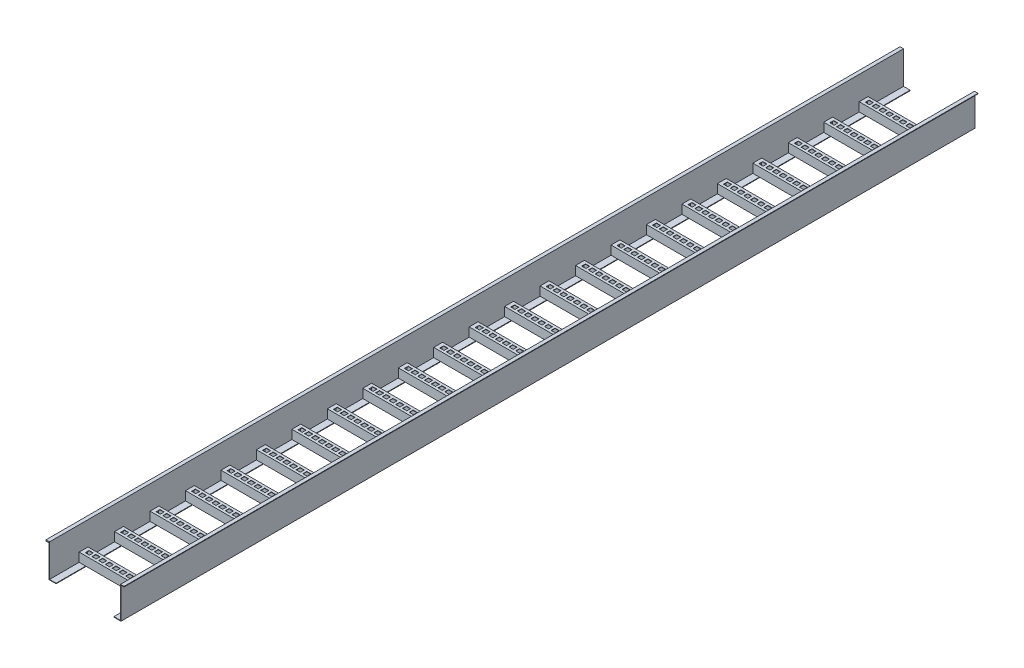
SolidWorks part; units mm, degrees
ref_plane "Alzado" through (0, 0, 0) normal (0, 0, 1) x (1, 0, 0)
ref_plane "Planta" through (0, 0, 0) normal (0, 1, 0) x (1, 0, 0)
ref_plane "Vista lateral" through (0, 0, 0) normal (1, 0, 0) x (0, 0, -1)
sketch "Croquis1" plane through (0, 0, 0) normal (0, 0, 1) x (1, 0, 0)
  line L0 (-55.6522, 79.8913) -> (-45.6522, 79.8913)
  line L1 (-45.6522, 79.8913) -> (-45.6522, -11.9155)
  line L2 (-45.6522, -11.9155) -> (154.3478, -11.9155)
  line L3 (154.3478, -11.9155) -> (154.3478, 76.1279)
  line L4 (154.3478, 76.1279) -> (164.3478, 76.1279)
  line L5 (164.3478, 76.1279) -> (164.3478, 74.6279)
  line L6 (164.3478, 74.6279) -> (155.8478, 74.6279)
  line L7 (155.8478, 74.6279) -> (155.8478, -13.4155)
  line L8 (155.8478, -13.4155) -> (-47.1522, -13.4155)
  line L9 (-47.1522, -13.4155) -> (-47.1522, 76.5154)
  line L10 (-47.1522, 76.5154) -> (-55.6522, 76.5154)
  line L11 (-55.6522, 76.5154) -> (-55.6522, 79.8913)
  line L12 (-27.1522, -11.9155) -> (-27.1522, -13.4155)
  line L13 (135.8478, -11.9155) -> (135.8478, -13.4155)
  dimension "D1" = 200
  dimension "D2" = 10
  dimension "D3" = 10
  dimension "D4" = 1.5
  dimension "D5" = 1.5
  dimension "D6" = 1.5
  dimension "D7" = 1.5
  dimension "D8" = 20
  dimension "D9" = 20
extrude "Saliente-Extruir1" add sketch "Croquis1" along normal blind 2408.5 contours L2 L13 L8 L7 L6 L5 L4 L3 | L12 L2 L1 L0 L11 L10 L9 L8
sketch "Croquis2" plane through (155.8478, 0, 0) normal (1, 0, 0) x (0, 0, -1)
  line L1 (-125, -11.9155) -> (-124, -11.9155)
  line L2 (-125, -11.9155) -> (-125, 13.0845)
  line L3 (-125, 13.0845) -> (-100, 13.0845)
  line L4 (-100, -11.9155) -> (-100, 13.0845)
  line L5 (-125, -11.9155) -> (-100, 13.0845) construction
  line L6 (-125, 13.0845) -> (-100, -11.9155) construction
  line L7 (0, 74.6279) -> (0, -13.4155) construction
  line L8 (-124, -11.9155) -> (-124, 12.0845)
  line L9 (-124, 12.0845) -> (-101, 12.0845)
  line L10 (-101, 12.0845) -> (-101, -11.9155)
  line L11 (-101, -11.9155) -> (-100, -11.9155)
  point P0 (-112.5, 0.5845)
  point P9 (-237.5, 0.5845)
  point P16 (-362.5, 0.5845)
  dimension "D1" = 25
  dimension "D2" = 25
  dimension "D3" = 1
  dimension "D4" = 100
  dimension "D5" = 1
  dimension "D6" = 1
extrude "Saliente-Extruir2" add sketch "Croquis2" against normal up to surface (201.5 mm away) up to face at (-45.6522, 33.9879, 1204.25)
pattern_linear "MatrizL1" count 23 spacing 100 along (0, 0, 1) of "Saliente-Extruir2"
sketch "Croquis3" plane through (0, 13.0845, 0) normal (0, 1, 0) x (1, 0, 0)
  line L0 (154.3478, -125) -> (154.3478, -100) construction
  line L1 (147.3478, -107) -> (135.3478, -107)
  line L2 (147.3478, -107) -> (147.3478, -118)
  line L3 (147.3478, -118) -> (135.3478, -118)
  line L4 (135.3478, -107) -> (135.3478, -118)
  line L5 (147.3478, -107) -> (135.3478, -118) construction
  line L6 (147.3478, -118) -> (135.3478, -107) construction
  line L7 (135.8478, -125) -> (154.3478, -125) construction
  line L8 (-45.6522, -100) -> (154.3478, -100) construction
  line L9 (-45.6522, -125) -> (154.3478, -125) construction
  line L10 (128.3478, -107) -> (116.3478, -107)
  line L11 (128.3478, -107) -> (128.3478, -118)
  line L12 (128.3478, -118) -> (116.3478, -118)
  line L13 (116.3478, -107) -> (116.3478, -118)
  line L14 (128.3478, -107) -> (116.3478, -118) construction
  line L15 (128.3478, -118) -> (116.3478, -107) construction
  line L17 (109.3478, -107) -> (97.3478, -107)
  line L18 (109.3478, -107) -> (109.3478, -118)
  line L19 (109.3478, -118) -> (97.3478, -118)
  line L20 (97.3478, -107) -> (97.3478, -118)
  line L21 (109.3478, -107) -> (97.3478, -118) construction
  line L22 (109.3478, -118) -> (97.3478, -107) construction
  line L23 (90.3478, -107) -> (78.3478, -107)
  line L24 (90.3478, -107) -> (90.3478, -118)
  line L25 (90.3478, -118) -> (78.3478, -118)
  line L26 (78.3478, -107) -> (78.3478, -118)
  line L27 (90.3478, -107) -> (78.3478, -118) construction
  line L28 (90.3478, -118) -> (78.3478, -107) construction
  line L29 (71.3478, -107) -> (59.3478, -107)
  line L30 (71.3478, -107) -> (71.3478, -118)
  line L31 (71.3478, -118) -> (59.3478, -118)
  line L32 (59.3478, -107) -> (59.3478, -118)
  line L33 (71.3478, -107) -> (59.3478, -118) construction
  line L34 (71.3478, -118) -> (59.3478, -107) construction
  line L35 (40.3478, -107) -> (52.3478, -107)
  line L36 (40.3478, -107) -> (40.3478, -118)
  line L37 (40.3478, -118) -> (52.3478, -118)
  line L38 (52.3478, -107) -> (52.3478, -118)
  line L39 (40.3478, -107) -> (52.3478, -118) construction
  line L40 (40.3478, -118) -> (52.3478, -107) construction
  line L41 (21.3478, -107) -> (33.3478, -107)
  line L42 (21.3478, -107) -> (21.3478, -118)
  line L43 (21.3478, -118) -> (33.3478, -118)
  line L44 (33.3478, -107) -> (33.3478, -118)
  line L45 (21.3478, -107) -> (33.3478, -118) construction
  line L46 (21.3478, -118) -> (33.3478, -107) construction
  line L47 (2.3478, -107) -> (14.3478, -107)
  line L48 (2.3478, -107) -> (2.3478, -118)
  line L49 (2.3478, -118) -> (14.3478, -118)
  line L50 (14.3478, -107) -> (14.3478, -118)
  line L51 (2.3478, -107) -> (14.3478, -118) construction
  line L52 (2.3478, -118) -> (14.3478, -107) construction
  line L53 (-16.6522, -107) -> (-4.6522, -107)
  line L54 (-16.6522, -107) -> (-16.6522, -118)
  line L55 (-16.6522, -118) -> (-4.6522, -118)
  line L56 (-4.6522, -107) -> (-4.6522, -118)
  line L57 (-16.6522, -107) -> (-4.6522, -118) construction
  line L58 (-16.6522, -118) -> (-4.6522, -107) construction
  line L59 (-35.6522, -107) -> (-23.6522, -107)
  line L60 (-35.6522, -107) -> (-35.6522, -118)
  line L61 (-35.6522, -118) -> (-23.6522, -118)
  line L62 (-23.6522, -107) -> (-23.6522, -118)
  line L63 (-35.6522, -107) -> (-23.6522, -118) construction
  line L64 (-35.6522, -118) -> (-23.6522, -107) construction
  point P0 (141.3478, -112.5)
  point P11 (122.3478, -112.5)
  point P18 (103.3478, -112.5)
  point P23 (84.3478, -112.5)
  point P28 (65.3478, -112.5)
  point P33 (46.3478, -112.5)
  point P38 (27.3478, -112.5)
  point P43 (8.3478, -112.5)
  point P48 (-10.6522, -112.5)
  point P53 (-29.6522, -112.5)
  dimension "D1" = 7
  dimension "D2" = 7
  dimension "D3" = 7
  dimension "D4" = 12
  dimension "D5" = 7
  dimension "D6" = 7
  dimension "D7" = 12
  dimension "D8" = 7
  dimension "D9" = 12
  dimension "D10" = 7
  dimension "D11" = 7
  dimension "D12" = 7
  dimension "D13" = 7
  dimension "D14" = 7
  dimension "D15" = 7
  dimension "D16" = 12
  dimension "D17" = 7
  dimension "D18" = 7
  dimension "D19" = 7
  dimension "D20" = 12
  dimension "D21" = 7
  dimension "D22" = 12
  dimension "D23" = 7
  dimension "D24" = 12
  dimension "D25" = 7
  dimension "D26" = 12
  dimension "D27" = 7
  dimension "D28" = 12
  dimension "D29" = 7
  dimension "D30" = 12
extrude "Cortar-Extruir1" cut sketch "Croquis3" against normal blind 25
pattern_linear "MatrizL2" count 50 spacing 100 along (0, 0, 1) of "Cortar-Extruir1"
